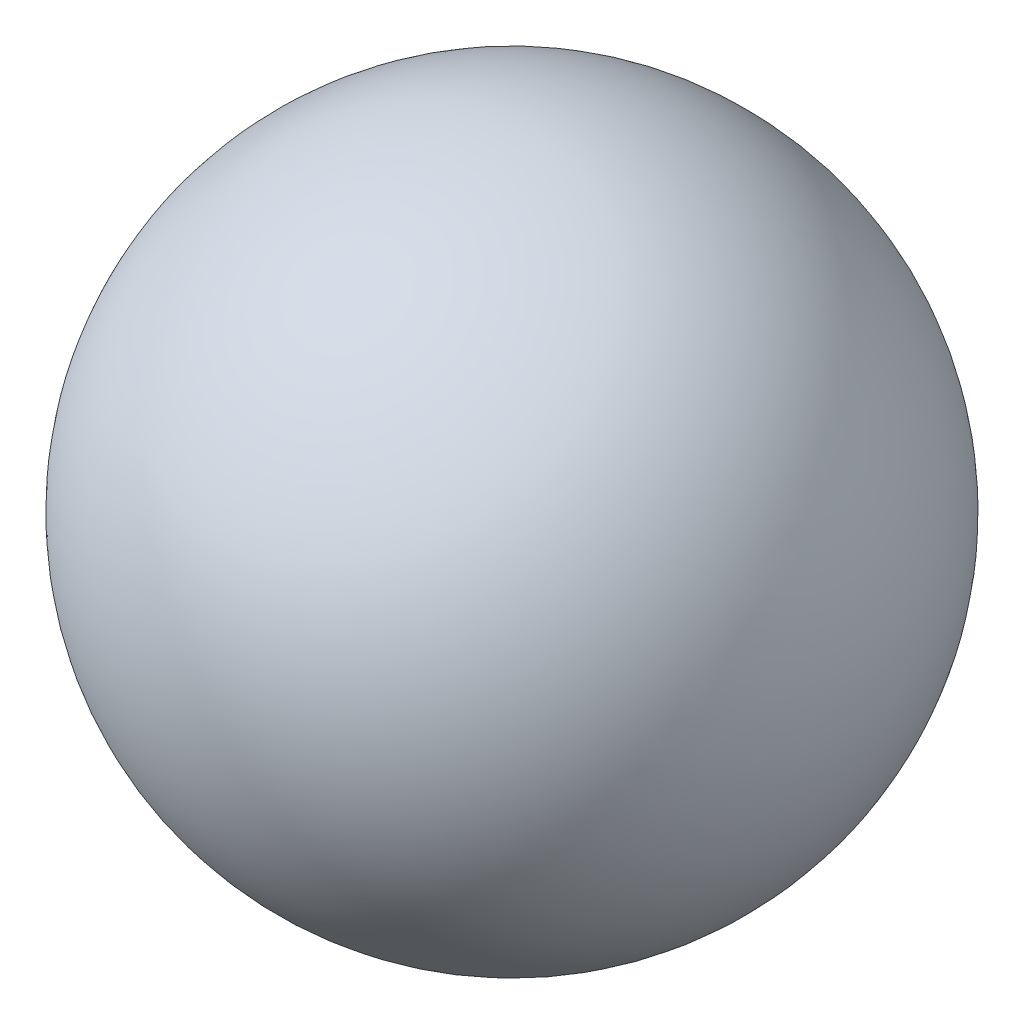
SolidWorks part; units mm, degrees
ref_plane "前视基准面" through (0, 0, 0) normal (0, 0, 1) x (1, 0, 0)
ref_plane "上视基准面" through (0, 0, 0) normal (0, 1, 0) x (1, 0, 0)
ref_plane "右视基准面" through (0, 0, 0) normal (1, 0, 0) x (0, 0, -1)
sketch "草图1" plane through (0, 0, 0) normal (0, 0, 1) x (1, 0, 0)
  line L0 (0, 0) -> (13.6627, 0) construction
  line L1 (-6, 0) -> (6, 0)
  circle A0 centre (0, 0) radius 6 construction
  arc A1 (6, 0) -> (-6, 0) centre (0, 0) ccw
  dimension "D1" = 12
revolve "旋转10" add sketch "草图1" angle 360 about L0
